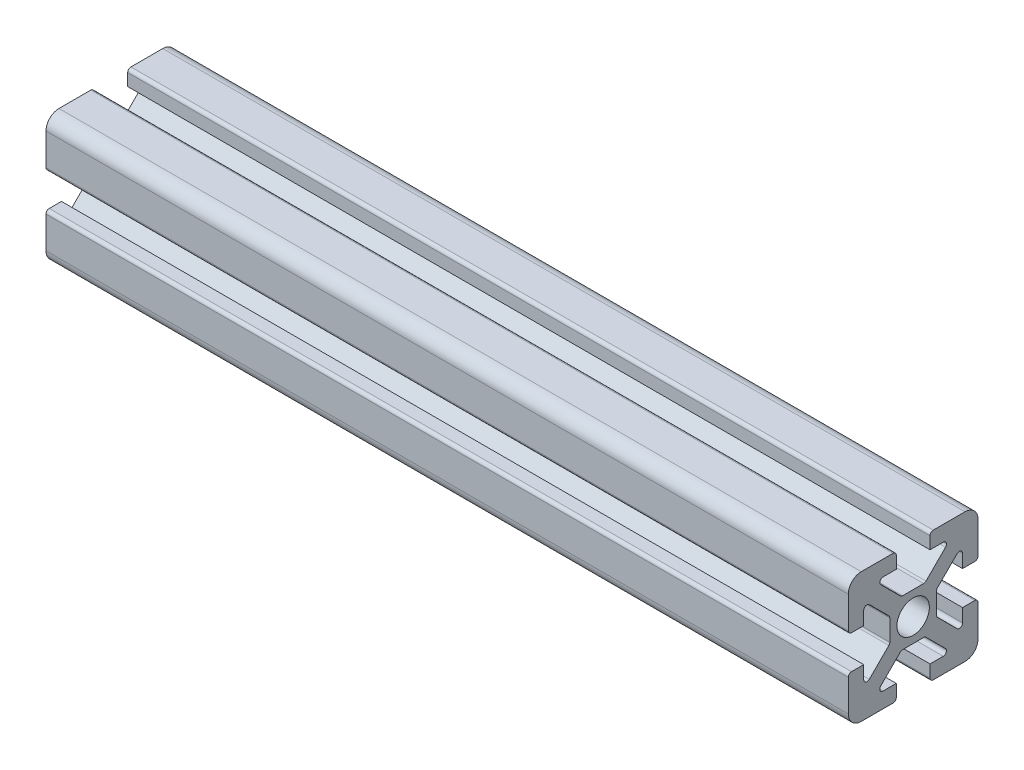
SolidWorks part; units mm, degrees
ref_plane "Front Plane" through (0, 0, 0) normal (0, 0, 1) x (1, 0, 0)
ref_plane "Top Plane" through (0, 0, 0) normal (0, 1, 0) x (1, 0, 0)
ref_plane "Right Plane" through (0, 0, 0) normal (1, 0, 0) x (0, 0, -1)
sketch "Sketch1" plane through (0, 0, 0) normal (1, 0, 0) x (0, 0, -1)
  line L0 (-2.6, 10) -> (-2.6, 7.6178)
  line L1 (10, -10) -> (2.6, -10)
  line L2 (10, -10) -> (10, -2.6)
  line L3 (10, 10) -> (2.6, 10)
  line L4 (-10, -10) -> (-10, -2.6)
  line L5 (10, -10) -> (-10, 10) construction
  line L6 (10, 10) -> (-10, -10) construction
  line L7 (-2.6, 7.6178) -> (-5.85, 7.6178)
  line L8 (-5.85, 7.6178) -> (-1.8322, 3.6)
  line L9 (-1.8322, 3.6) -> (1.8322, 3.6)
  line L10 (0, 0) -> (0, 10) construction
  line L11 (5.85, 7.6178) -> (1.8322, 3.6)
  line L12 (2.6, 7.6178) -> (5.85, 7.6178)
  line L13 (2.6, 10) -> (2.6, 7.6178)
  line L14 (10, 2.6) -> (7.6178, 2.6)
  line L15 (7.6178, 2.6) -> (7.6178, 5.85)
  line L16 (7.6178, 5.85) -> (3.6, 1.8322)
  line L17 (3.6, 1.8322) -> (3.6, -1.8322)
  line L18 (7.6178, -5.85) -> (3.6, -1.8322)
  line L19 (7.6178, -2.6) -> (7.6178, -5.85)
  line L20 (10, -2.6) -> (7.6178, -2.6)
  line L21 (2.6, -10) -> (2.6, -7.6178)
  line L22 (2.6, -7.6178) -> (5.85, -7.6178)
  line L23 (5.85, -7.6178) -> (1.8322, -3.6)
  line L24 (1.8322, -3.6) -> (-1.8322, -3.6)
  line L25 (-5.85, -7.6178) -> (-1.8322, -3.6)
  line L26 (-2.6, -7.6178) -> (-5.85, -7.6178)
  line L27 (-2.6, -10) -> (-2.6, -7.6178)
  line L28 (-10, -2.6) -> (-7.6178, -2.6)
  line L29 (-7.6178, -2.6) -> (-7.6178, -5.85)
  line L30 (-7.6178, -5.85) -> (-3.6, -1.8322)
  line L31 (-3.6, -1.8322) -> (-3.6, 1.8322)
  line L32 (-7.6178, 5.85) -> (-3.6, 1.8322)
  line L33 (-7.6178, 2.6) -> (-7.6178, 5.85)
  line L34 (-10, 2.6) -> (-7.6178, 2.6)
  line L35 (0, 0) -> (3.6, 0) construction
  line L36 (-2.6, 10) -> (-10, 10)
  line L37 (10, 2.6) -> (10, 10)
  line L38 (-2.6, -10) -> (-10, -10)
  line L39 (-10, 2.6) -> (-10, 10)
  circle A0 centre (0, 0) radius 2.5
  point P0 (0, 0)
  point P19 (0, 3.6)
  point P27 (3.6, 0)
  point P36 (0, -3.6)
  point P45 (-3.6, 0)
  point P48 (0, 0)
  dimension "D2" = 5
  dimension "D1" = 20
  dimension "D3" = 5.85
  dimension "D4" = 2.6
  dimension "D5" = 6.4
  dimension "D6" = 1.25
  dimension "D7" = 4
extrude "Boss-Extrude1" add sketch "Sketch1" along normal mid plane 123.698
fillet "Fillet1" radius 2 4 edges at (0, -10, -10) (0, -10, 10) (0, 10, -10) (0, 10, 10)
fillet "Fillet2" radius 0.5 24 edges at (0, -2.6, -10) (0, 2.6, -10) (0, -10, -2.6) (0, -10, 2.6) (0, 10, 2.6) (0, 10, -2.6) (0, -2.6, 10) (0, 2.6, 10) (0, -1.8322, -3.6) (0, 1.8322, -3.6) (0, 5.85, -7.6178) (0, -5.85, -7.6178) (0, -7.6178, 5.85) (0, -3.6, 1.8322) (0, -7.6178, -5.85) (0, -3.6, -1.8322) (0, -1.8322, 3.6) (0, 1.8322, 3.6) (0, 5.85, 7.6178) (0, -5.85, 7.6178) (0, 3.6, -1.8322) (0, 3.6, 1.8322) (0, 7.6178, 5.85) (0, 7.6178, -5.85)
